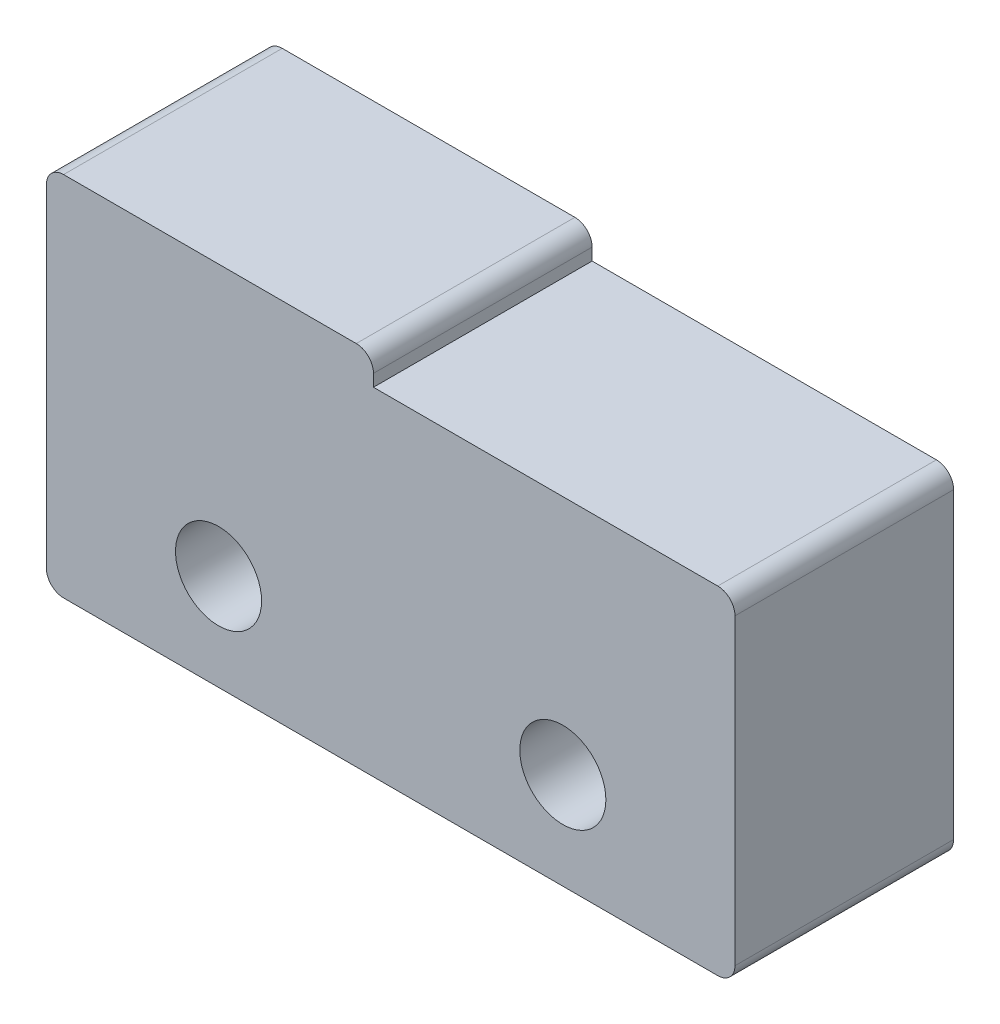
SolidWorks part; units mm, degrees
ref_plane "Front Plane" through (0, 0, 0) normal (0, 0, 1) x (1, 0, 0)
ref_plane "Top Plane" through (0, 0, 0) normal (0, 1, 0) x (1, 0, 0)
ref_plane "Right Plane" through (0, 0, 0) normal (1, 0, 0) x (0, 0, -1)
sketch "Sketch1" plane through (0, 0, 0) normal (0, 0, 1) x (1, 0, 0)
  line L0 (10, 4.8) -> (-0.5, 4.8)
  line L2 (10, 4.8) -> (10, -5)
  line L3 (10, -5) -> (-10, -5)
  line L4 (-10, 5.65) -> (-10, -5)
  line L5 (9.6, 4.8) -> (-10, -5) construction
  line L6 (10, -5) -> (-10, 5) construction
  line L7 (-0.5, 5.65) -> (-10, 5.65)
  line L8 (-0.5, 5.65) -> (-0.5, 4.8)
  line L9 (-10, 5) -> (-10, -5) construction
  line L10 (-0.5, 5) -> (-0.5, -5) construction
  line L12 (10, 4.8) -> (-10, 4.8) construction
  line L13 (10, 5.65) -> (-10, 5.65) construction
  circle A0 centre (-5, -2.2) radius 1.25
  circle A1 centre (5, -2.2) radius 1.25
  point P0 (0, 0)
  dimension "D1" = 9.8
  dimension "D2" = 10.65
  dimension "D3" = 9.5
extrude "Boss-Extrude1" add sketch "Sketch1" along normal blind 6.35
fillet "Fillet1" radius 0.5 5 edges at (10, -5, 3.175) (10, 4.8, 3.175) (-10, -5, 3.175) (-10, 5.65, 3.175) (-0.5, 5.65, 3.175)
